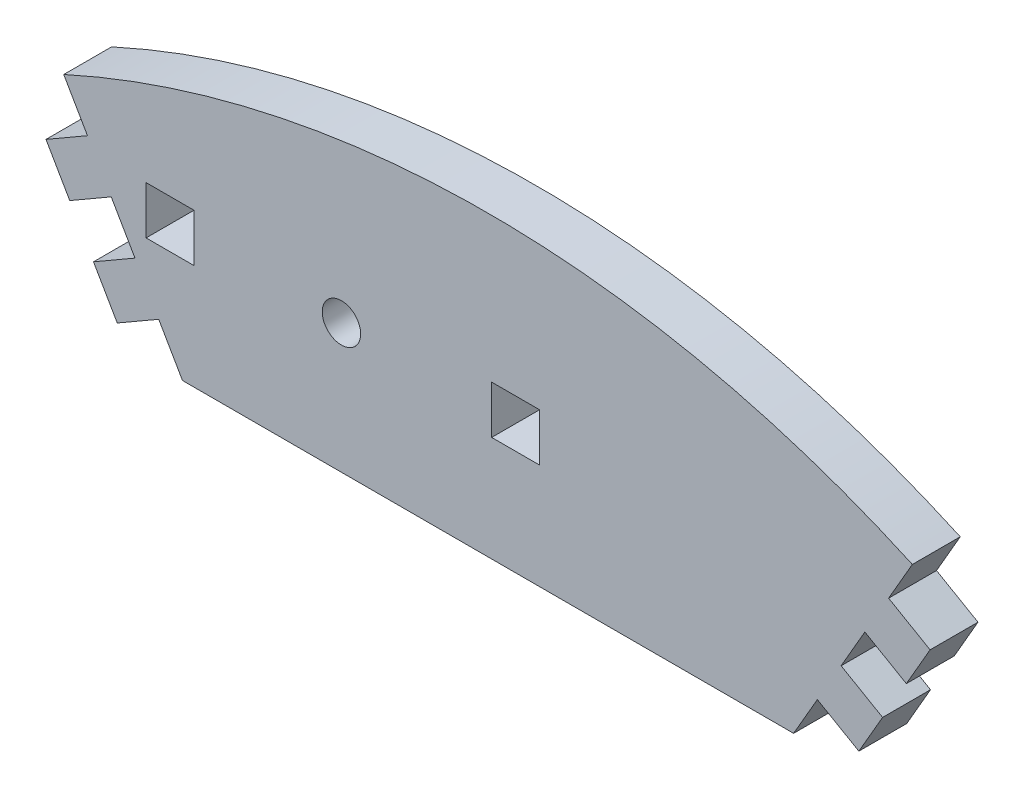
SolidWorks part; units mm, degrees
ref_plane "Front Plane" through (0, 0, 0) normal (0, 0, 1) x (1, 0, 0)
ref_plane "Top Plane" through (0, 0, 0) normal (0, 1, 0) x (1, 0, 0)
ref_plane "Right Plane" through (0, 0, 0) normal (1, 0, 0) x (0, 0, -1)
sketch "Sketch1" plane through (0, 0, 0) normal (0, 0, 1) x (1, 0, 0)
  line L0 (-32.85, 77.9867) -> (32.85, 77.9867)
  line L4 (-32.85, 77.9867) -> (-35.403, 82.4086)
  line L5 (0, 0) -> (0, 126.1957) construction
  line L7 (32.85, 77.9867) -> (35.403, 82.4086)
  line L8 (35.403, 82.4086) -> (39.863, 79.8336)
  line L9 (39.863, 79.8336) -> (42.416, 84.2555)
  line L10 (42.416, 84.2555) -> (37.956, 86.8305)
  line L11 (37.956, 86.8305) -> (40.509, 91.2525)
  line L12 (40.509, 91.2525) -> (44.969, 88.6775)
  line L13 (44.969, 88.6775) -> (47.522, 93.0994)
  line L14 (47.522, 93.0994) -> (43.062, 95.6744)
  line L15 (43.062, 95.6744) -> (45.615, 100.0963)
  line L16 (-43.062, 95.6744) -> (-45.615, 100.0963)
  line L17 (-47.522, 93.0994) -> (-43.062, 95.6744)
  line L18 (-44.969, 88.6775) -> (-47.522, 93.0994)
  line L19 (-40.509, 91.2525) -> (-44.969, 88.6775)
  line L20 (-37.956, 86.8305) -> (-40.509, 91.2525)
  line L21 (-42.416, 84.2555) -> (-37.956, 86.8305)
  line L22 (-39.863, 79.8336) -> (-42.416, 84.2555)
  line L23 (-35.403, 82.4086) -> (-39.863, 79.8336)
  arc A0 (-45.615, 100.0963) -> (45.615, 100.0963) centre (0, 0) cw
  dimension "D1" = 120
  dimension "D2" = 110
  dimension "D3" = 25.53
  dimension "D4" = 5.15
  dimension "D5" = 65.7
extrude "Boss-Extrude1" add sketch "Sketch1" along normal blind 5.15
sketch "Sketch2" plane through (0, 0, 5.15) normal (0, 0, 1) x (1, 0, 0)
  line L0 (0, 111.5372) -> (0, 71.5875) construction
  line L1 (0, -55) -> (0, 55) construction
  line L3 (0.39, 94.4578) -> (5.54, 94.4578)
  line L4 (0.39, 94.4578) -> (0.39, 89.3078)
  line L5 (0.39, 89.3078) -> (5.54, 89.3078)
  line L6 (5.54, 94.4578) -> (5.54, 89.3078)
  line L11 (-32.85, 77.9867) -> (-17.0875, 77.9867) construction
  line L12 (-32.85, 77.9867) -> (32.85, 77.9867) construction
  line L14 (-31.61, 89.3078) -> (-36.76, 89.3078)
  line L15 (-31.61, 89.3078) -> (-31.61, 94.4578)
  line L16 (-31.61, 94.4578) -> (-36.76, 94.4578)
  line L17 (-36.76, 89.3078) -> (-36.76, 94.4578)
  circle A0 centre (-15.76, 91.8974) radius 2.0675
  dimension "D4" = 4.135
  dimension "D1" = 32
  dimension "D2" = 5.15
  dimension "D3" = 5.15
  dimension "D5" = 15.7625
  dimension "D7" = 5.15
extrude "Cut-Extrude1" cut sketch "Sketch2" against normal through all
